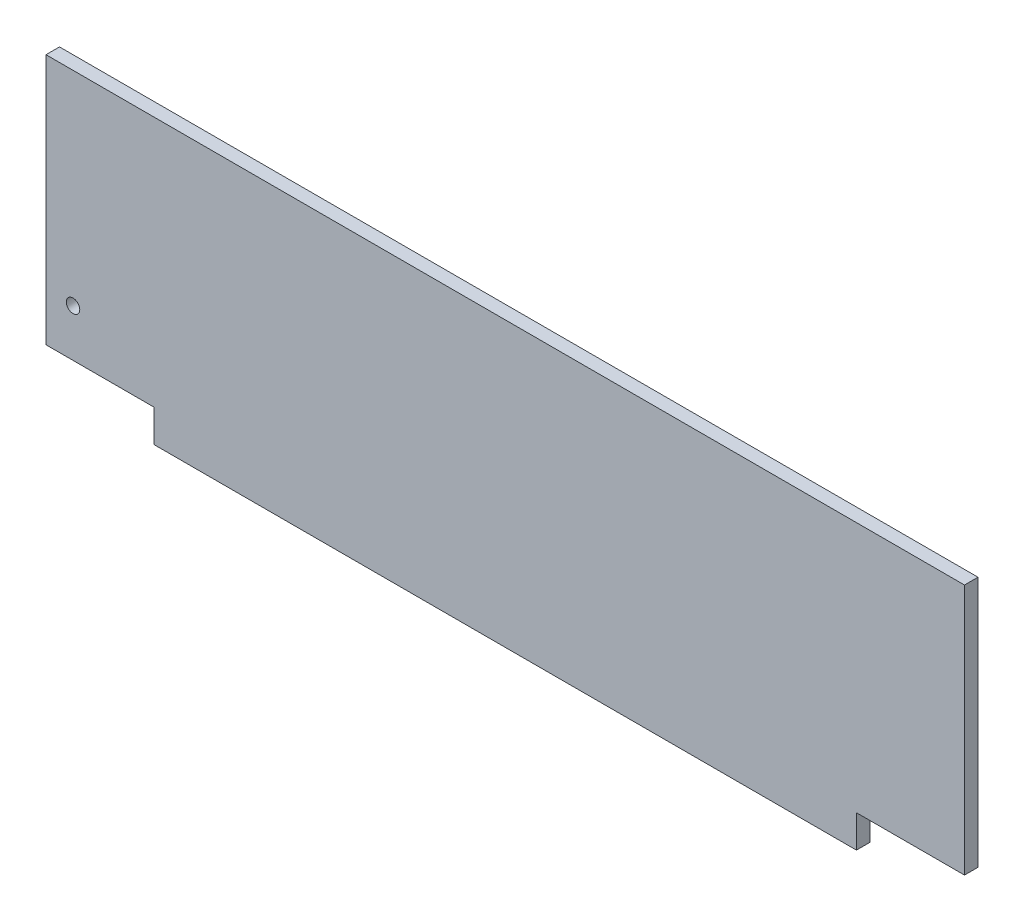
SolidWorks part; units mm, degrees
ref_plane "Plan de face" through (0, 0, 0) normal (0, 0, 1) x (1, 0, 0)
ref_plane "Plan de dessus" through (0, 0, 0) normal (0, 1, 0) x (1, 0, 0)
ref_plane "Plan de droite" through (0, 0, 0) normal (1, 0, 0) x (0, 0, -1)
sketch "Esquisse1" plane through (0, 0, 0) normal (0, 0, 1) x (1, 0, 0)
  line L1 (-340, 105) -> (340, 105)
  line L2 (-340, 105) -> (-340, -105)
  line L3 (-340, -105) -> (340, -105)
  line L4 (340, 105) -> (340, -105)
  dimension "D1" = 680
  dimension "D2" = 210
  dimension "D3" = 105
  dimension "D4" = 340
extrude "Boss.-Extru.1" add sketch "Esquisse1" along normal blind 10
sketch "Esquisse2" plane through (0, 0, 10) normal (0, 0, 1) x (1, 0, 0)
  line L1 (-340, -105) -> (-260, -105)
  line L2 (-340, -105) -> (-340, -81)
  line L3 (-340, -81) -> (-260, -81)
  line L4 (-260, -105) -> (-260, -81)
  line L5 (340, -105) -> (260, -105)
  line L6 (340, -105) -> (340, -81)
  line L7 (340, -81) -> (260, -81)
  line L8 (260, -105) -> (260, -81)
  dimension "D1" = 80
  dimension "D2" = 80
  dimension "D3" = 24
  dimension "D4" = 24
extrude "Enlèv. mat.-Extru.1" cut sketch "Esquisse2" against normal through all
sketch "Esquisse3" plane through (0, 0, 10) normal (0, 0, 1) x (1, 0, 0)
  line L0 (-340, 105) -> (-340, -81) construction
  line L1 (-260, -81) -> (-340, -81) construction
  circle A0 centre (-320, -46) radius 5
  dimension "D1" = 10
  dimension "D2" = 20
  dimension "D3" = 35
extrude "Enlèv. mat.-Extru.2" cut sketch "Esquisse3" against normal through all
